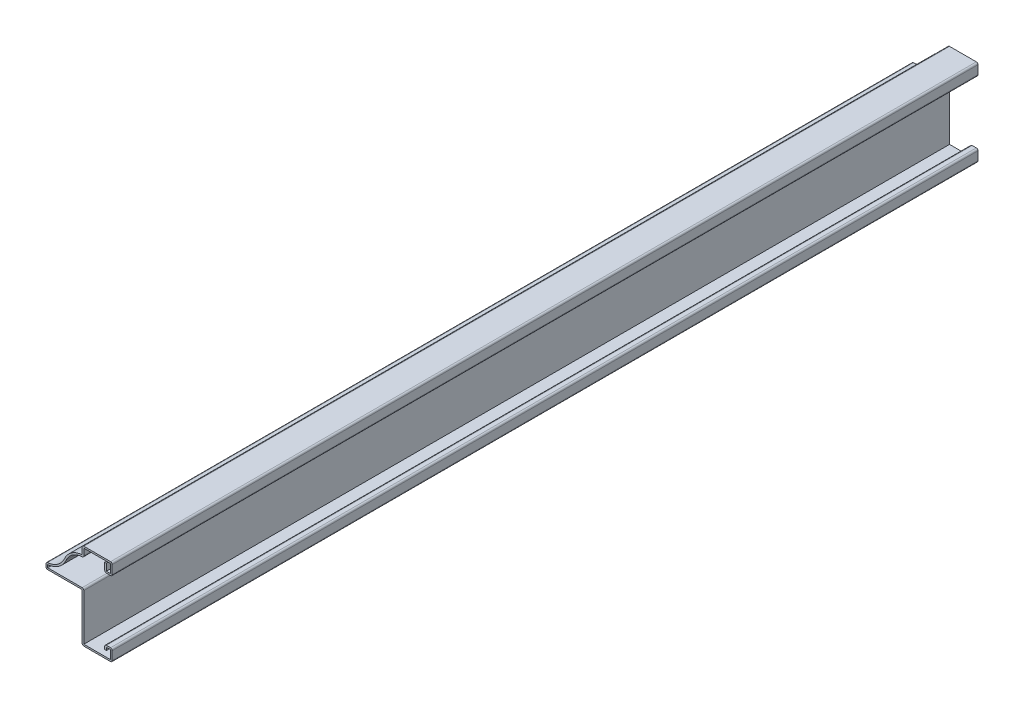
SolidWorks part; units mm, degrees
ref_plane "Front Plane" through (0, 0, 0) normal (0, 0, 1) x (1, 0, 0)
ref_plane "Top Plane" through (0, 0, 0) normal (0, 1, 0) x (1, 0, 0)
ref_plane "Right Plane" through (0, 0, 0) normal (1, 0, 0) x (0, 0, -1)
sketch "Sketch1" plane through (0, 0, 0) normal (0, 0, 1) x (1, 0, 0)
  line L0 (-3.9687, 3.9688) -> (-3.9687, 6.35)
  line L1 (-3.9687, 6.35) -> (0, 6.35)
  line L2 (0, 6.35) -> (0, 0)
  line L3 (0, 0) -> (-15.875, 0)
  line L4 (-15.875, 0) -> (-15.875, 25.4)
  line L5 (-15.875, 25.4) -> (-34.925, 25.4)
  line L6 (-34.925, 25.4) -> (-34.925, 28.575)
  line L7 (-15.875, 41.275) -> (-15.875, 45.6406)
  line L8 (-15.875, 45.6406) -> (0, 45.6406)
  line L9 (0, 45.6406) -> (0, 39.2906)
  line L10 (0, 39.2906) -> (-3.9687, 39.2906)
  line L11 (-3.9687, 39.2906) -> (-3.9688, 43.8626)
  arc A0 (-34.925, 28.575) -> (-25.1361, 34.9315) centre (-34.925, 39.2906) ccw
  arc A1 (-25.1361, 34.9315) -> (-15.875, 41.275) centre (-15.3472, 30.5724) cw
  point P13 (-25.6886, 35.0417)
  point P19 (0, 0)
  dimension "D11" = 10.7156
  dimension "D1" = 45.6406
  dimension "D2" = 34.925
  dimension "D3" = 15.875
  dimension "D4" = 6.35
  dimension "D5" = 4.3656
  dimension "D6" = 12.7
  dimension "D7" = 3.175
  dimension "D8" = 6.35
  dimension "D9" = 3.9688
  dimension "D10" = 2.3813
  dimension "D12" = 15.875
  dimension "D13" = 1.778
extrude "Extrude-Thin1" add sketch "Sketch1" against normal blind 456.4062 thin
fillet "Fillet1" radius 0.889 12 edges at (0, 0, -228.2031) (-3.9687, 6.35, -228.2031) (0, 6.35, -228.2031) (-15.875, 0, -228.2031) (-14.986, 26.289, -228.2031) (-34.925, 25.4, -228.2031) (-34.925, 28.575, -228.2031) (-3.9687, 39.2906, -228.2031) (-14.986, 40.3924, -228.2031) (-15.875, 45.6406, -228.2031) (0, 39.2906, -228.2031) (0, 45.6406, -228.2031)
